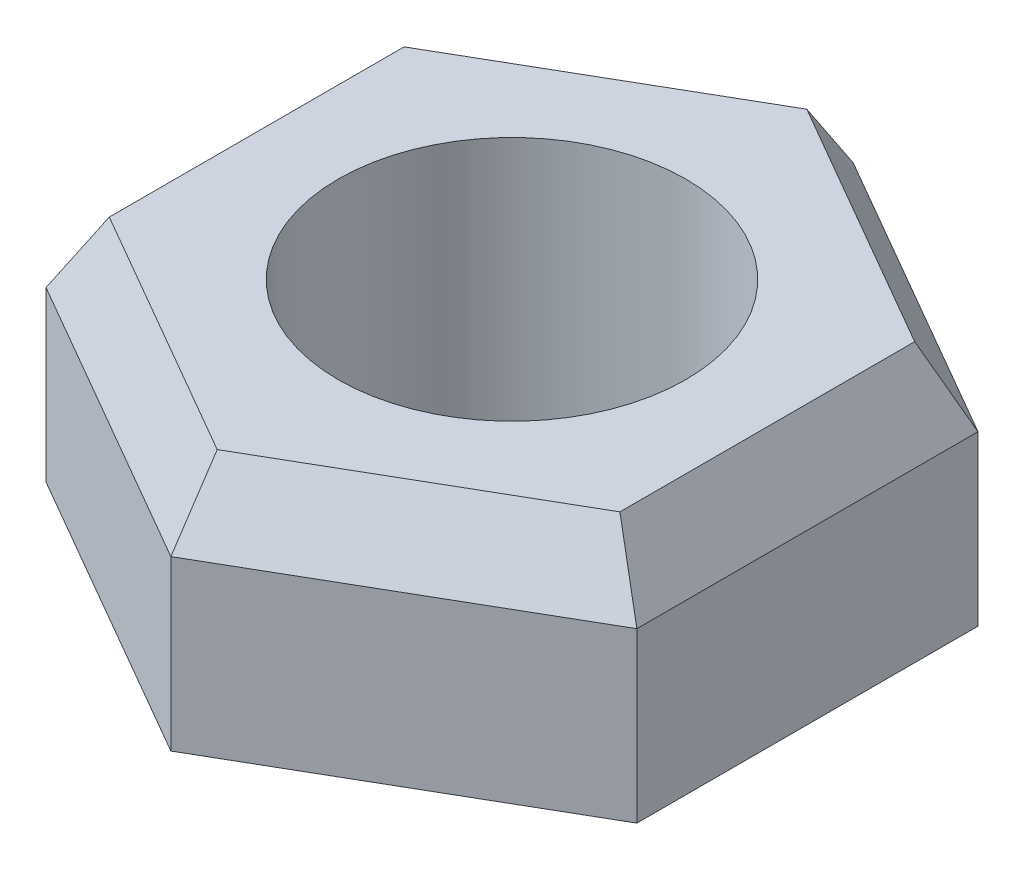
SolidWorks part; units mm, degrees
ref_plane "Спереди" through (0, 0, 0) normal (0, 0, 1) x (1, 0, 0)
ref_plane "Сверху" through (0, 0, 0) normal (0, 1, 0) x (1, 0, 0)
ref_plane "Справа" through (0, 0, 0) normal (1, 0, 0) x (0, 0, -1)
sketch "Эскиз1" plane through (0, 0, 0) normal (0, 1, 0) x (1, 0, 0)
  line L1 (8.5, -4.9075) -> (8.5, 4.9075)
  line L2 (8.5, 4.9075) -> (0, 9.815)
  line L3 (0, 9.815) -> (-8.5, 4.9075)
  line L4 (-8.5, 4.9075) -> (-8.5, -4.9075)
  line L5 (-8.5, -4.9075) -> (0, -9.815)
  line L6 (0, -9.815) -> (8.5, -4.9075)
  circle A0 centre (0, 0) radius 8.5 construction
  circle A1 centre (0, 0) radius 5
extrude "Бобышка-Вытянуть1" add sketch "Эскиз1" along normal blind 8
chamfer "Фаска1" distance 2 angle 30 12 edges at (4.25, 0, -7.3612) (8.5, 0, 0) (4.25, 0, 7.3612) (-4.25, 0, 7.3612) (-8.5, 0, 0) (-4.25, 0, -7.3612) (4.25, 8, 7.3612) (8.5, 8, 0) (4.25, 8, -7.3612) (-4.25, 8, -7.3612) (-8.5, 8, 0) (-4.25, 8, 7.3612)
